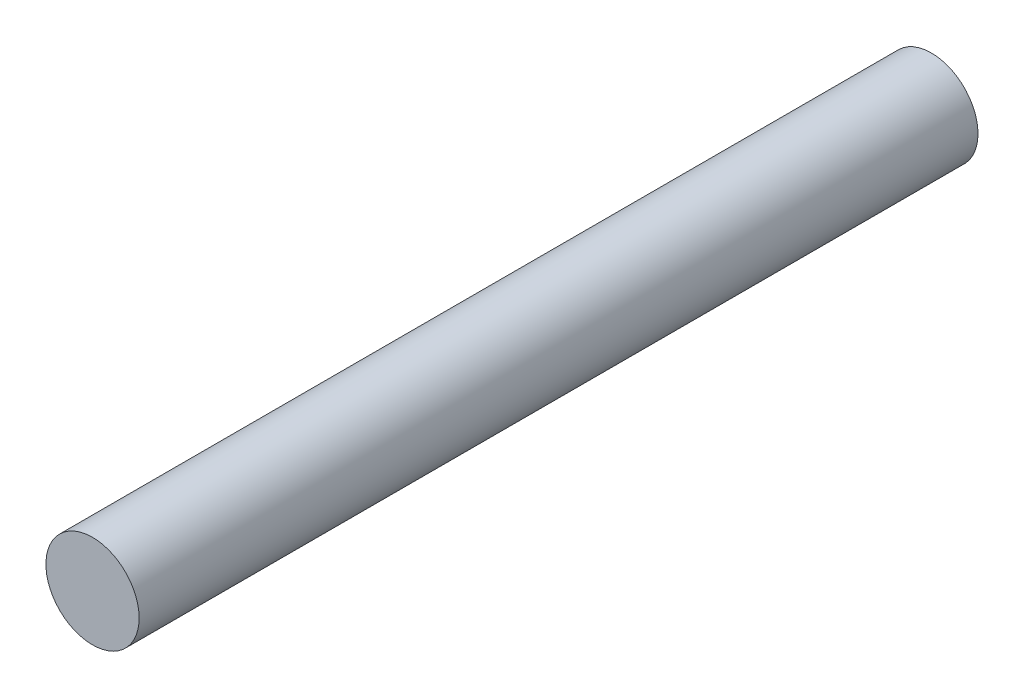
SolidWorks part; units mm, degrees
material "AISI 304"
ref_plane "Front Plane" through (0, 0, 0) normal (0, 0, 1) x (1, 0, 0)
ref_plane "Top Plane" through (0, 0, 0) normal (0, 1, 0) x (1, 0, 0)
ref_plane "Right Plane" through (0, 0, 0) normal (1, 0, 0) x (0, 0, -1)
sketch "Sketch1" plane through (0, 0, 0) normal (0, 0, 1) x (1, 0, 0)
  circle A0 centre (0, 0) radius 1
  dimension "D1" = 2
extrude "Boss-Extrude1" add sketch "Sketch1" along normal mid plane 18
